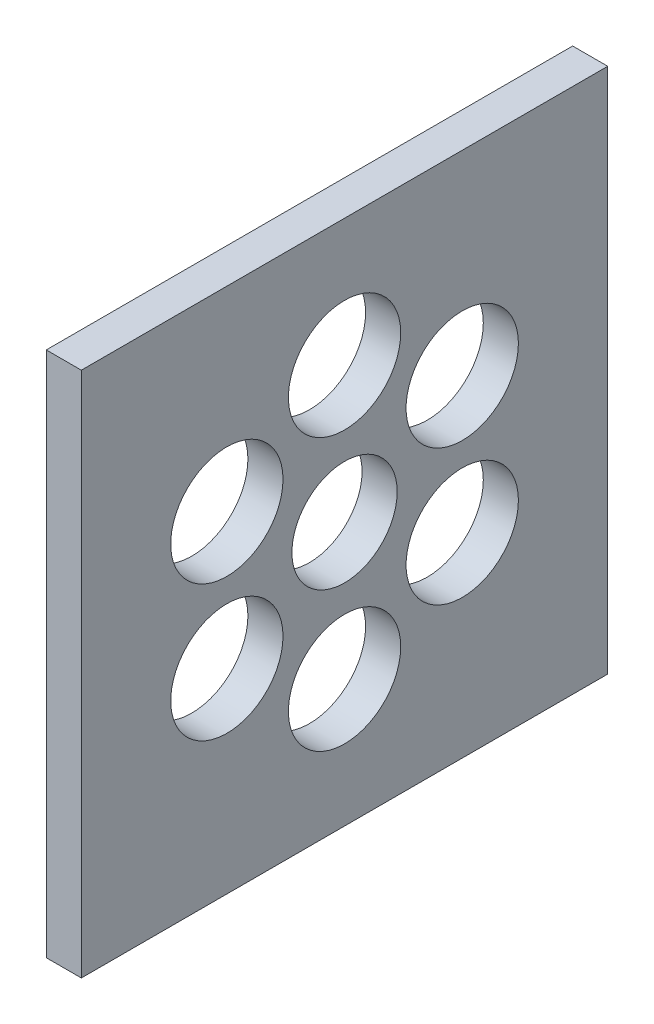
SolidWorks part; units mm, degrees
ref_plane "Front Plane" through (0, 0, 0) normal (0, 0, 1) x (1, 0, 0)
ref_plane "Top Plane" through (0, 0, 0) normal (0, 1, 0) x (1, 0, 0)
ref_plane "Right Plane" through (0, 0, 0) normal (1, 0, 0) x (0, 0, -1)
sketch "Sketch1" plane through (0, 0, 0) normal (1, 0, 0) x (0, 0, -1)
  line L1 (-75, 75) -> (75, 75)
  line L2 (-75, 75) -> (-75, -75)
  line L3 (-75, -75) -> (75, -75)
  line L4 (75, 75) -> (75, -75)
  line L5 (-75, 75) -> (75, -75) construction
  line L6 (-75, -75) -> (75, 75) construction
  point P0 (0, 0)
  dimension "D1" = 150
  dimension "D2" = 150
extrude "Boss-Extrude1" add sketch "Sketch1" along normal blind 10
sketch "Sketch2" plane through (10, 0, 0) normal (1, 0, 0) x (0, 0, -1)
  circle A0 centre (0, 0) radius 15
  circle A1 centre (0, 38.7277) radius 16
  circle A2 centre (33.5392, 19.3639) radius 16
  circle A3 centre (33.5392, -19.3639) radius 16
  circle A4 centre (0, -38.7277) radius 16
  circle A5 centre (-33.5392, -19.3639) radius 16
  circle A6 centre (-33.5392, 19.3639) radius 16
  point P18 (0, 0)
  dimension "D1" = 6
extrude "Cut-Extrude1" cut sketch "Sketch2" against normal blind 25
